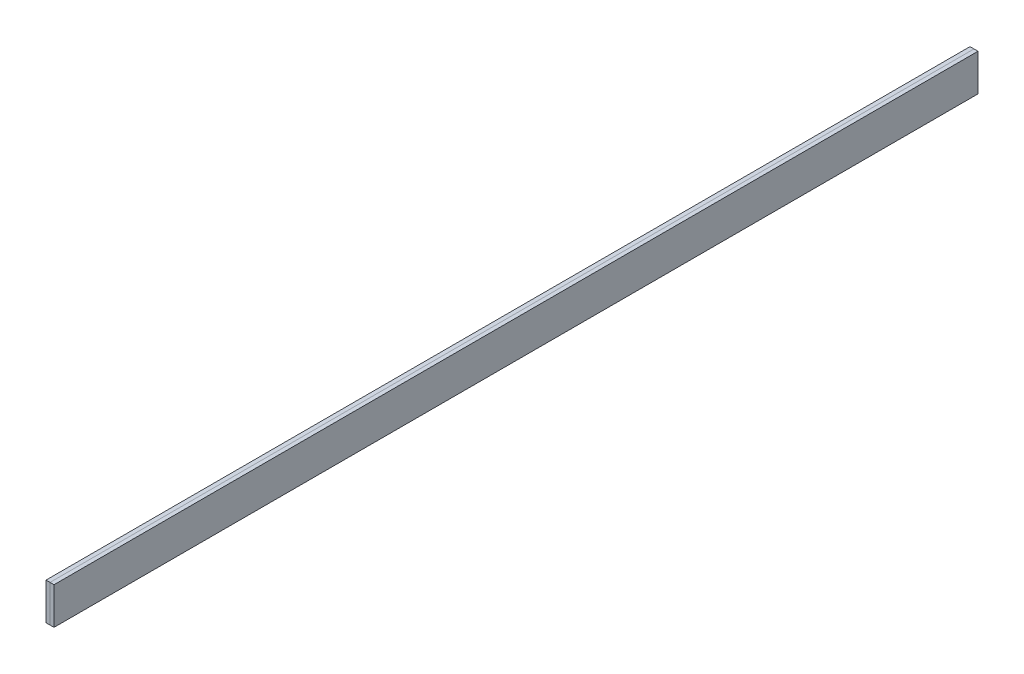
SolidWorks part; units mm, degrees
ref_plane "Front Plane" through (0, 0, 0) normal (0, 0, 1) x (1, 0, 0)
ref_plane "Top Plane" through (0, 0, 0) normal (0, 1, 0) x (1, 0, 0)
ref_plane "Right Plane" through (0, 0, 0) normal (1, 0, 0) x (0, 0, -1)
sketch "Sketch1" plane through (0, 0, 0) normal (0, 0, 1) x (1, 0, 0)
  line L1 (0, 0) -> (-0.65, 0)
  line L2 (0, 0) -> (0, 6)
  line L3 (0, 6) -> (-0.65, 6)
  line L4 (-0.65, 0) -> (-0.65, 6)
  line L5 (-0.325, 6) -> (-0.325, 0) construction
  line L6 (0, 3) -> (-0.65, 3) construction
  point P24 (-0.325, 3)
  dimension "D1" = 6
  dimension "D2" = 0.65
extrude "Boss-Extrude1" add sketch "Sketch1" along normal blind 150
mirror "Mirror2" about plane through (0, 0, 150) normal (-1, 0, 0) of bodies 101
